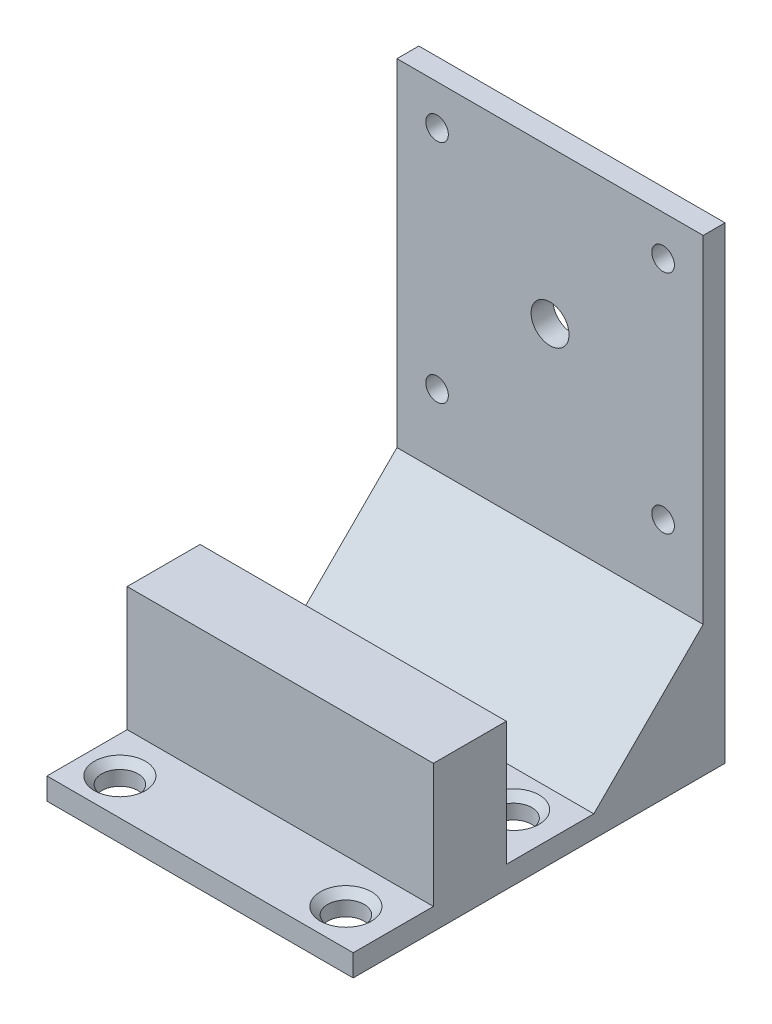
SolidWorks part; units mm, degrees
ref_plane "Plan de face" through (0, 0, 0) normal (0, 0, 1) x (1, 0, 0)
ref_plane "Plan de dessus" through (0, 0, 0) normal (0, 1, 0) x (1, 0, 0)
ref_plane "Plan de droite" through (0, 0, 0) normal (1, 0, 0) x (0, 0, -1)
sketch "Esquisse1" plane through (0, 0, 0) normal (0, 0, 1) x (1, 0, 0)
  line L0 (0, 42) -> (42, 0) construction
  line L1 (0, 0) -> (42, 0)
  line L2 (0, 0) -> (0, 42)
  line L3 (0, 42) -> (42, 42)
  line L4 (42, 0) -> (42, 42)
  line L5 (42, 42) -> (0, 0) construction
  line L7 (0, 0) -> (42, 0)
  line L8 (0, 0) -> (0, -22.2)
  line L9 (0, -22.2) -> (42, -22.2)
  line L10 (42, 0) -> (42, -22.2)
  circle A0 centre (5.5, 5.5) radius 1.55
  circle A1 centre (36.5, 5.5) radius 1.55
  circle A2 centre (36.5, 36.5) radius 1.55
  circle A3 centre (5.5, 36.5) radius 1.55
  circle A4 centre (21, 21) radius 2.6
  dimension "D5" = 3.1
  dimension "D8" = 5.2
  dimension "D1" = 42
  dimension "D2" = 42
  dimension "D3" = 5.5
  dimension "D4" = 5.5
  dimension "D9" = 43.2
  dimension "D6" = 2
  dimension "D7" = 2
extrude "Boss.-Extru.1" add sketch "Esquisse1" along normal blind 3 contours L1 L4 L3 L2 A4 A3 A2 A1 A0 | L10 L1 L8 L9
sketch "Esquisse2" plane through (0, 0, 3) normal (0, 0, 1) x (1, 0, 0)
  line L0 (42, -22.2) -> (42, 42) construction
  line L1 (0, -22.2) -> (42, -22.2)
  line L2 (0, -22.2) -> (0, -19.2)
  line L3 (0, -19.2) -> (42, -19.2)
  line L4 (42, -22.2) -> (42, -19.2)
  dimension "D1" = 3
extrude "Boss.-Extru.2" add sketch "Esquisse2" along normal blind 48
sketch "Esquisse3" plane through (42, 0, 0) normal (1, 0, 0) x (0, 0, -1)
  line L0 (-3, -4.2) -> (-18, -19.2)
  line L1 (-3, -19.2) -> (-3, 42) construction
  line L2 (-51, -19.2) -> (-3, -19.2) construction
  line L3 (-3, -4.2) -> (-3, -19.2)
  line L4 (-3, -19.2) -> (-18, -19.2)
  dimension "D1" = 45
  dimension "D2" = 15
extrude "Boss.-Extru.3" add sketch "Esquisse3" against normal up to surface (42 mm away) up to face at (0, 0.2, 18)
sketch "Esquisse4" plane through (0, -19.2, 0) normal (0, 1, 0) x (1, 0, 0)
  line L0 (0, -18) -> (42, -18) construction
  line L1 (0, -51) -> (0, -18) construction
  circle A0 centre (5, -23) radius 2.5
  circle A1 centre (36, -23) radius 2.5
  circle A2 centre (36, -46) radius 2.5
  circle A3 centre (5, -46) radius 2.5
  dimension "D1" = 5
  dimension "D2" = 5
  dimension "D3" = 5
  dimension "D4" = 2
  dimension "D5" = 2
extrude "Enlèv. mat.-Extru.4" cut sketch "Esquisse4" against normal up to next
chamfer "Chanfrein1" distance 1 angle 45 4 edges at (36, -19.2, 48.5) (5, -19.2, 48.5) (5, -19.2, 25.5) (36, -19.2, 25.5)
sketch "Esquisse5" plane through (0, -19.2, 0) normal (0, 1, 0) x (1, 0, 0)
  line L0 (0, -51) -> (0, -18) construction
  line L1 (0, -30) -> (42, -30)
  line L2 (0, -30) -> (0, -40)
  line L3 (0, -40) -> (42, -40)
  line L4 (42, -30) -> (42, -40)
  line L5 (42, -51) -> (42, -18) construction
  line L6 (0, -18) -> (42, -18) construction
  point P8 (0, -35)
  dimension "D1" = 5
  dimension "D2" = 12
extrude "Boss.-Extru.4" add sketch "Esquisse5" along normal blind 17
